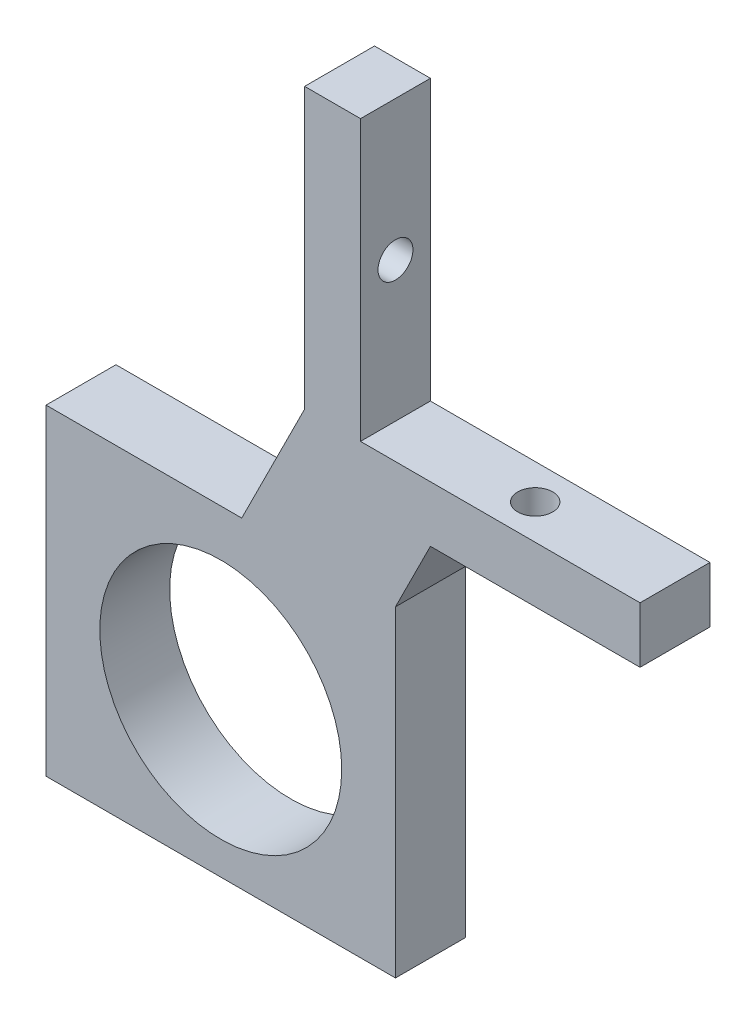
SolidWorks part; units mm, degrees
ref_plane "Front Plane" through (0, 0, 0) normal (0, 0, 1) x (1, 0, 0)
ref_plane "Top Plane" through (0, 0, 0) normal (0, 1, 0) x (1, 0, 0)
ref_plane "Right Plane" through (0, 0, 0) normal (1, 0, 0) x (0, 0, -1)
sketch "Sketch1" plane through (0, 0, 0) normal (0, 0, 1) x (1, 0, 0)
  line L0 (-16.51, -33.02) -> (-16.51, -5.08) construction
  line L1 (2.54, 33.02) -> (-2.54, 33.02)
  line L2 (2.54, 33.02) -> (2.54, -33.02)
  line L3 (2.54, -33.02) -> (-2.54, -33.02)
  line L4 (-2.54, 33.02) -> (-2.54, -33.02)
  line L5 (2.54, 33.02) -> (-2.54, -33.02) construction
  line L6 (2.54, -33.02) -> (-2.54, 33.02) construction
  line L7 (-2.54, -33.02) -> (-30.48, -33.02)
  line L8 (-2.54, -33.02) -> (-2.54, -5.08)
  line L9 (-2.54, -5.08) -> (-30.48, -5.08)
  line L10 (-30.48, -33.02) -> (-30.48, -5.08)
  point P0 (0, 0)
  point P11 (-16.51, -19.05)
  dimension "D1" = 52.07
  dimension "D2" = 33.02
  dimension "D3" = 5.08
extrude "Boss-Extrude1" add sketch "Sketch1" along normal blind 6.35 contours L10 L7 L4 L9 | L1 L4 L3 L2
sketch "Sketch2" plane through (-2.54, 0, 0) normal (-1, 0, 0) x (0, 0, 1)
  line L0 (6.35, 33.02) -> (0, 33.02) construction
  line L1 (2.5081, 33.02) -> (2.5081, 7.62) construction
  circle A0 centre (3.175, 20.32) radius 1.5875
  point P4 (3.175, 33.02)
  point P8 (2.5081, 20.32)
  dimension "D1" = 3.175
  dimension "D2" = 25.4
extrude "Cut-Extrude1" cut sketch "Sketch2" against normal blind 12.7
sketch "Sketch3" plane through (2.54, 0, 0) normal (1, 0, 0) x (0, 0, -1)
  line L0 (-6.35, 33.02) -> (-6.35, -33.02) construction
  line L1 (-6.35, 7.62) -> (0, 7.62)
  line L2 (-6.35, 7.62) -> (-6.35, 2.54)
  line L3 (-6.35, 2.54) -> (0, 2.54)
  line L4 (0, 7.62) -> (0, 2.54)
  line L5 (0, 33.02) -> (0, -33.02) construction
  line L6 (-6.35, 33.02) -> (0, 33.02) construction
  dimension "D1" = 5.08
  dimension "D2" = 25.4
extrude "Boss-Extrude2" add sketch "Sketch3" along normal blind 25.4
sketch "Sketch4" plane through (0, 2.54, 0) normal (0, -1, 0) x (1, 0, 0)
  line L0 (2.54, 3.175) -> (27.94, 3.175) construction
  line L1 (2.54, 6.35) -> (2.54, 0) construction
  line L2 (27.94, 6.35) -> (27.94, 0) construction
  circle A0 centre (15.24, 3.175) radius 1.5875
  point P10 (27.94, 3.175)
  point P13 (15.24, 3.175)
  dimension "D1" = 3.175
extrude "Cut-Extrude2" cut sketch "Sketch4" against normal blind 25.4
sketch "Sketch5" plane through (0, 0, 6.35) normal (0, 0, 1) x (1, 0, 0)
  line L0 (-2.54, -5.08) -> (-2.54, -33.02) construction
  line L1 (2.54, -33.02) -> (-30.48, -33.02) construction
  line L2 (-30.48, -4.6691) -> (-2.54, -4.6691) construction
  line L3 (-30.48, -33.02) -> (-30.48, -5.08) construction
  circle A0 centre (-10.16, -19.05) radius 10.9918
  point P11 (13.3948, -18.415)
  point P12 (-22.4752, -18.3664)
  point P13 (-2.54, -19.05)
  point P14 (0, 0)
  point P15 (-16.51, -4.6691)
  dimension "D1" = 21.9837
  dimension "D2" = 6.35
extrude "Cut-Extrude3" cut sketch "Sketch5" against normal blind 25.4
sketch "Sketch6" plane through (0, 0, 6.35) normal (0, 0, 1) x (1, 0, 0)
  line L0 (-2.54, 7.62) -> (-8.89, -5.08)
  line L1 (-2.54, 33.02) -> (-2.54, -5.08) construction
  line L2 (-2.54, -5.08) -> (-30.48, -5.08) construction
  line L3 (-2.54, 7.62) -> (-2.54, -5.08)
  line L4 (-2.54, -5.08) -> (-8.89, -5.08)
  line L5 (2.54, 2.54) -> (2.54, -10.16)
  line L6 (2.54, 2.54) -> (2.54, -33.02) construction
  line L7 (2.54, -10.16) -> (8.89, 2.54)
  line L8 (27.94, 2.54) -> (2.54, 2.54) construction
  line L9 (8.89, 2.54) -> (2.54, 2.54)
  dimension "D1" = 6.35
extrude "Boss-Extrude3" add sketch "Sketch6" against normal up to surface (6.35 mm away) up to face at (0.8319, -19.05, 0)
sketch "Sketch7" plane through (0, -5.08, 0) normal (0, 1, 0) x (1, 0, 0)
  line L0 (-30.48, -3.175) -> (-8.89, -3.175) construction
  line L1 (-30.48, -6.35) -> (-30.48, 0) construction
  line L2 (-8.89, 0) -> (-8.89, -6.35) construction
sketch "Sketch8" plane through (0, 0, 6.35) normal (0, 0, 1) x (1, 0, 0)
  line L0 (2.54, -33.02) -> (-30.48, -33.02) construction
  line L6 (-26.035, -19.05) -> (5.715, -19.05) construction
  line L7 (-26.035, -3.81) -> (5.715, -3.81)
  line L8 (-26.035, -3.81) -> (-26.035, -33.02)
  line L9 (-26.035, -33.02) -> (5.715, -33.02)
  line L10 (5.715, -3.81) -> (5.715, -33.02)
  line L11 (2.54, -10.16) -> (8.89, 2.54) construction
  circle A0 centre (-10.16, -19.05) radius 10.9918
  circle A1 centre (-10.16, -19.05) radius 10.9918 construction
  point P11 (-10.16, -19.05)
  point P12 (-10.16, -19.05)
  dimension "D1" = 31.75
extrude "Boss-Extrude4" add sketch "Sketch8" against normal up to surface (6.35 mm away) up to face at (0, 0.635, 0)
sketch "Sketch9" plane through (0, 0, 6.35) normal (0, 0, 1) x (1, 0, 0)
  line L1 (-26.035, -5.08) -> (-30.48, -5.08)
  line L2 (-26.035, -5.08) -> (-26.035, -33.02)
  line L3 (-26.035, -33.02) -> (-30.48, -33.02)
  line L4 (-30.48, -5.08) -> (-30.48, -33.02)
extrude "Cut-Extrude4" cut sketch "Sketch9" against normal up to surface (6.35 mm away) up to face at (-3.2204, 0.4536, 0)
